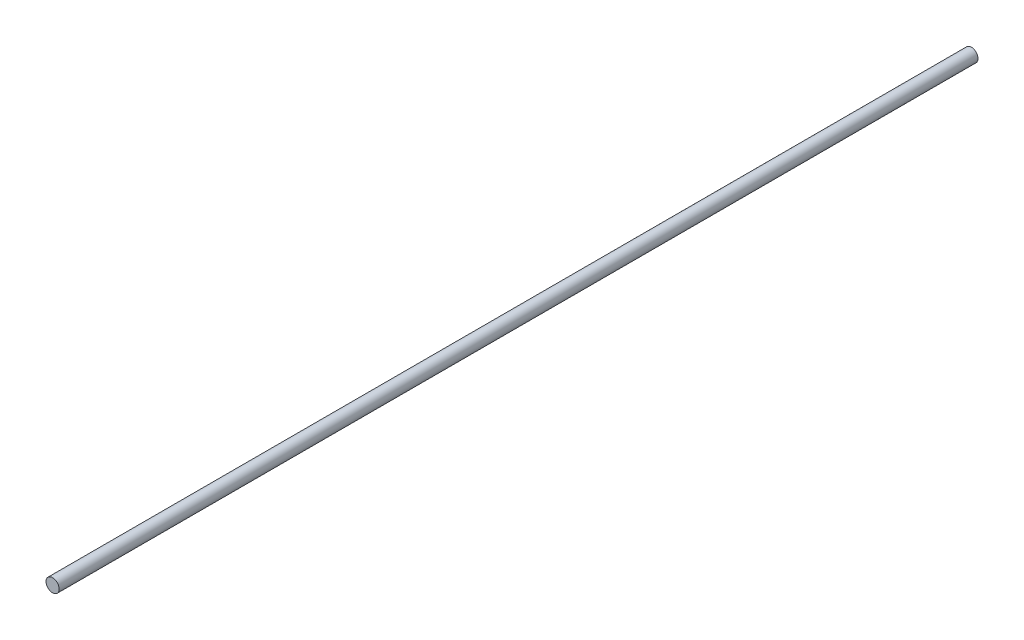
SolidWorks part; units mm, degrees
ref_plane "Front Plane" through (0, 0, 0) normal (0, 0, 1) x (1, 0, 0)
ref_plane "Top Plane" through (0, 0, 0) normal (0, 1, 0) x (1, 0, 0)
ref_plane "Right Plane" through (0, 0, 0) normal (1, 0, 0) x (0, 0, -1)
sketch "Sketch1" plane through (0, 0, 0) normal (0, 0, 1) x (1, 0, 0)
  circle A0 centre (0, 0) radius 4
  dimension "D1" = 8
extrude "Boss-Extrude1" add sketch "Sketch1" along normal blind 558.8
